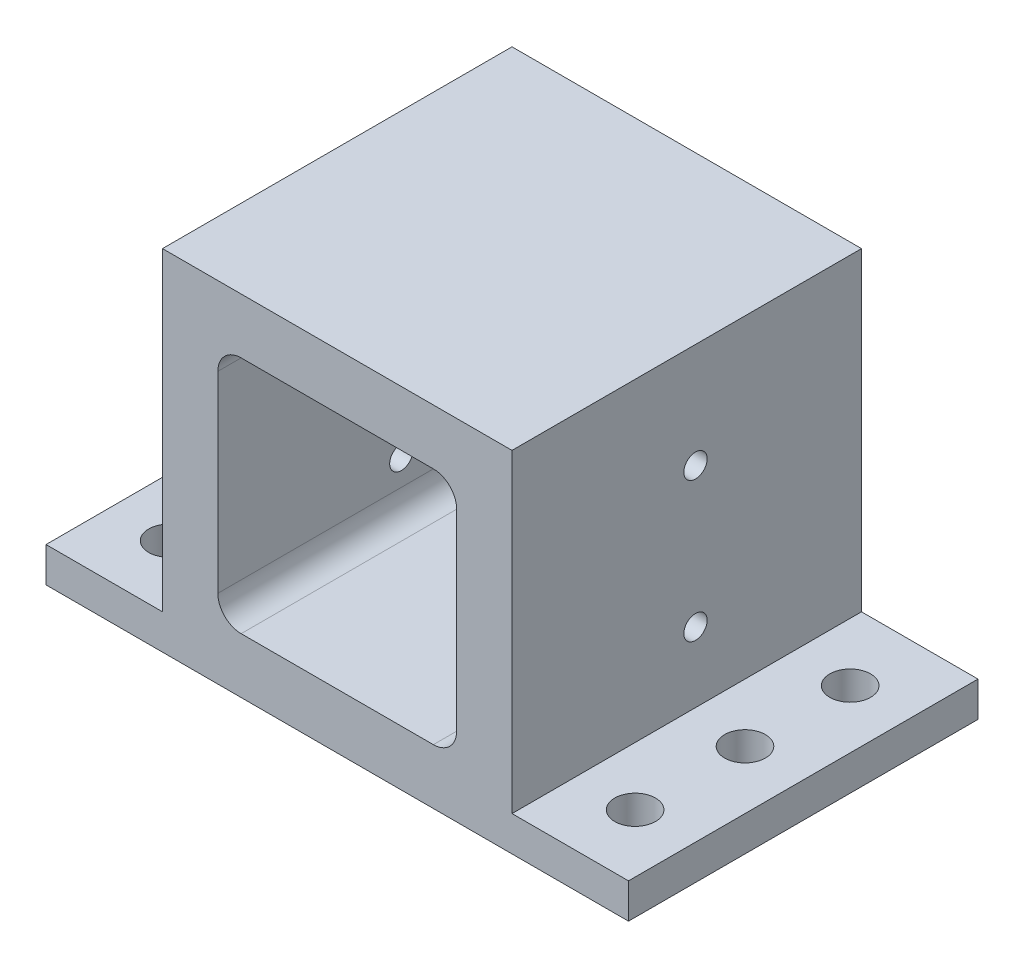
SolidWorks part; units mm, degrees
ref_plane "Plan de face" through (0, 0, 0) normal (0, 0, 1) x (1, 0, 0)
ref_plane "Plan de dessus" through (0, 0, 0) normal (0, 1, 0) x (1, 0, 0)
ref_plane "Plan de droite" through (0, 0, 0) normal (1, 0, 0) x (0, 0, -1)
sketch "Esquisse1" plane through (0, 0, 0) normal (0, 0, 1) x (1, 0, 0)
  line L0 (0, 0) -> (-60, 0)
  line L1 (-60, 0) -> (-60, -54)
  line L2 (-60, -54) -> (-80, -54)
  line L3 (-80, -54) -> (-80, -60)
  line L6 (20, -60) -> (20, -54)
  line L7 (20, -54) -> (0, -54)
  line L8 (0, -54) -> (0, 0)
  line L9 (-80, -60) -> (20, -60)
  dimension "D1" = 100
  dimension "D2" = 20
  dimension "D3" = 20
  dimension "D4" = 6
  dimension "D5" = 54
  dimension "D6" = 6
extrude "Boss.-Extru.1" add sketch "Esquisse1" against normal blind 60
sketch "Esquisse2" plane through (0, 0, 0) normal (0, 0, 1) x (1, 0, 0)
  line L0 (0, 0) -> (-60, 0) construction
  line L1 (-50.5, -9.5) -> (-9.5, -9.5)
  line L2 (-50.5, -9.5) -> (-50.5, -50.5)
  line L3 (-50.5, -50.5) -> (-9.5, -50.5)
  line L4 (-9.5, -9.5) -> (-9.5, -50.5)
  line L5 (-60, 0) -> (-60, -54) construction
  dimension "D1" = 41
  dimension "D2" = 41
  dimension "D3" = 9.5
  dimension "D4" = 9.5
extrude "Enlèv. mat.-Extru.1" cut sketch "Esquisse2" against normal blind 50
fillet "Congé1" radius 4 4 edges at (-9.5, -9.5, -25) (-9.5, -50.5, -25) (-50.5, -50.5, -25) (-50.5, -9.5, -25)
sketch "Esquisse4" plane through (0, -60, 0) normal (0, -1, 0) x (1, 0, 0)
  line L0 (-70, 0) -> (-70, -60) construction
  line L1 (-80, 0) -> (20, 0) construction
  line L2 (-80, -60) -> (20, -60) construction
  line L3 (-30, 0) -> (-30, -60) construction
  line L4 (-80, -60) -> (-80, 0) construction
  circle A0 centre (-70, -11.1343) radius 3.5
  circle A1 centre (-70, -30) radius 3.5
  circle A2 centre (-70, -48.0521) radius 3.5
  circle A3 centre (10, -48.0521) radius 3.5
  circle A4 centre (10, -30) radius 3.5
  circle A5 centre (10, -11.1343) radius 3.5
  dimension "D2" = 7
  dimension "D3" = 7
  dimension "D4" = 7
  dimension "D1" = 10
extrude "Enlèv. mat.-Extru.2" cut sketch "Esquisse4" against normal through all
sketch "Esquisse6" plane through (-60, 0, 0) normal (-1, 0, 0) x (0, 0, 1)
  line L0 (-60, 0) -> (0, 0) construction
  circle A0 centre (-31.5004, -18) radius 2
  circle A1 centre (-31.5004, -42) radius 2
  dimension "D3" = 4
  dimension "D4" = 4
  dimension "D1" = 18
  dimension "D2" = 24
extrude "Enlèv. mat.-Extru.4" cut sketch "Esquisse6" against normal through all
sketch "Esquisse7" plane through (0, 0, -50) normal (0, 0, 1) x (1, 0, 0)
  line L0 (-50.5, -13.5) -> (-50.5, -46.5) construction
  line L1 (-13.5, -9.5) -> (-46.5, -9.5) construction
  circle A0 centre (-30, -17.5) radius 1.35
  dimension "D1" = 2.7
  dimension "D2" = 20.5
  dimension "D3" = 8
extrude "Enlèv. mat.-Extru.5" cut sketch "Esquisse7" against normal through all
